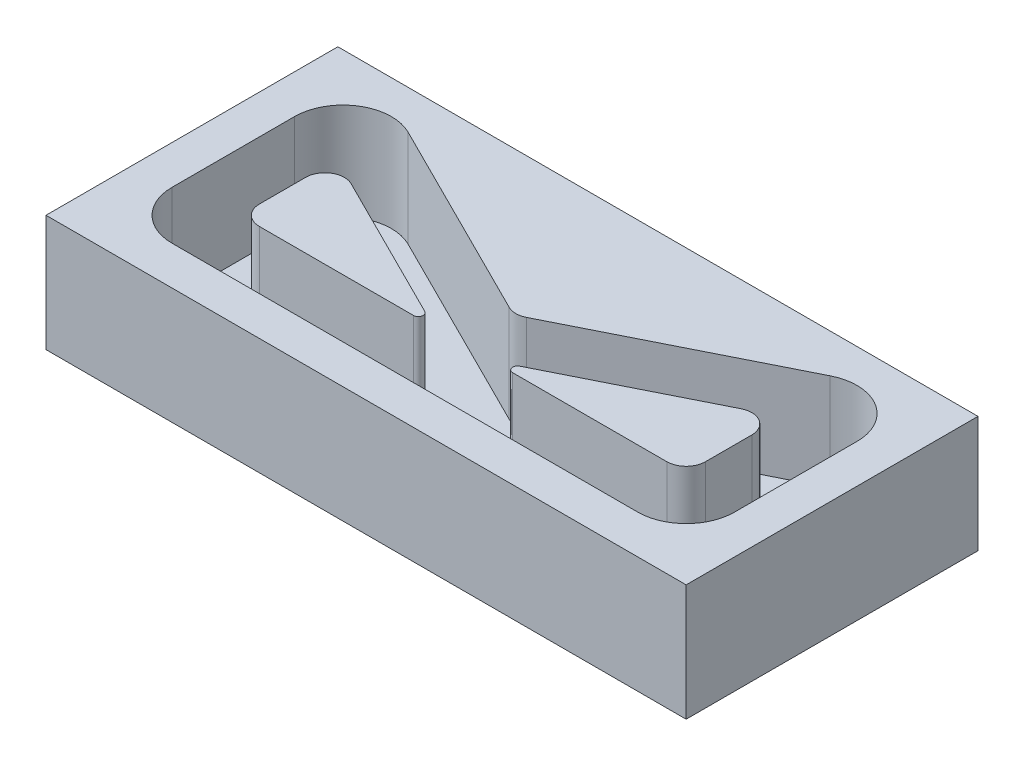
SolidWorks part; units mm, degrees
ref_plane "Front Plane" through (0, 0, 0) normal (0, 0, 1) x (1, 0, 0)
ref_plane "Top Plane" through (0, 0, 0) normal (0, 1, 0) x (1, 0, 0)
ref_plane "Right Plane" through (0, 0, 0) normal (1, 0, 0) x (0, 0, -1)
sketch "Sketch1" plane through (0, 0, 0) normal (0, 1, 0) x (1, 0, 0)
  line L0 (-0.9472, 0.4736) -> (-8.5528, 4.2764)
  line L1 (-10, 3.382) -> (-10, 1)
  line L2 (-9, 0) -> (-1.059, 0)
  line L3 (1.0528, 2.8277) -> (-9.382, 8.0451)
  line L4 (-13, 5.809) -> (-13, -0.5)
  line L5 (-10.5, -3) -> (13.5, -3)
  line L6 (-13, -3) -> (12.7082, -3) construction
  line L7 (-13, 9.8541) -> (-13, -3) construction
  line L8 (12.7082, -3) -> (-13, 9.8541) construction
  line L9 (-10, 5) -> (-10, 0) construction
  line L10 (0, 0) -> (-10, 5) construction
  line L11 (-10, 0) -> (0, 0) construction
  line L12 (1.5, 15.2524) -> (1.5, -18.7374) construction
  line L13 (12, 0) -> (4.059, 0)
  line L14 (3.9472, 0.4736) -> (11.5528, 4.2764)
  line L15 (1.9472, 2.8277) -> (12.382, 8.0451)
  line L16 (13, 3.382) -> (13, 1)
  line L17 (16, 5.809) -> (16, -0.5)
  line L18 (12.382, 8.0451) -> (-9.382, 8.0451) construction
  line L19 (-0.2764, 1.8152) -> (-7.882, 5.618) construction
  line L20 (-15, -5) -> (18, -5)
  line L21 (-15, -5) -> (-15, 10.0451)
  line L22 (-15, 10.0451) -> (18, 10.0451)
  line L23 (-12.9787, 6.1343) -> (1.5, -4.1568) construction
  line L24 (1.5, -4.1568) -> (15.9787, 6.1343) construction
  line L25 (18, -5) -> (18, 10.0451)
  line L26 (-15, -5) -> (18, 10.0451) construction
  line L27 (-15, 10.0451) -> (18, -5) construction
  line L28 (-11.5, 3.382) -> (-11.5, 1) construction
  line L29 (-9, -1.5) -> (-1.059, -1.5) construction
  line L30 (3.2764, 1.8152) -> (10.882, 5.618)
  line L31 (14.5, 3.382) -> (14.5, 1)
  line L32 (12, -1.5) -> (4.059, -1.5)
  circle A0 centre (1.5, 0.5061) radius 1.5831 construction
  circle A1 centre (-10.9351, 6.1728) radius 1.5 construction
  circle A2 centre (-11.0512, -1.07) radius 1.5 construction
  arc A3 (-10.5, -3) -> (-13, -0.5) centre (-10.5, -0.5) cw
  arc A4 (-9.382, 8.0451) -> (-13, 5.809) centre (-10.5, 5.809) ccw
  arc A5 (-10, 3.382) -> (-8.5528, 4.2764) centre (-9, 3.382) cw
  arc A6 (-9, 0) -> (-10, 1) centre (-9, 1) cw
  circle A7 centre (-4.84, -1.5) radius 1.5 construction
  circle A8 centre (-4.1195, 3.7368) radius 1.5 construction
  circle A9 centre (-11.5, 2.3936) radius 1.5 construction
  circle A10 centre (14.5, 2.3936) radius 1.5 construction
  circle A11 centre (7.1195, 3.7368) radius 1.5 construction
  circle A12 centre (7.84, -1.5) radius 1.5 construction
  circle A13 centre (14.0512, -1.07) radius 1.5 construction
  circle A14 centre (13.9351, 6.1728) radius 1.5 construction
  arc A15 (12, 0) -> (13, 1) centre (12, 1) ccw
  arc A16 (13, 3.382) -> (11.5528, 4.2764) centre (12, 3.382) ccw
  arc A17 (12.382, 8.0451) -> (16, 5.809) centre (13.5, 5.809) cw
  arc A18 (13.5, -3) -> (16, -0.5) centre (13.5, -0.5) ccw
  arc A19 (1.9472, 2.8277) -> (1.0528, 2.8277) centre (1.5, 3.7221) cw
  arc A20 (-1.059, 0) -> (-0.9472, 0.4736) centre (-1.059, 0.25) ccw
  arc A21 (3.9472, 0.4736) -> (4.059, 0) centre (4.059, 0.25) ccw
  arc A22 (-11.5, 3.382) -> (-7.882, 5.618) centre (-9, 3.382) cw construction
  arc A23 (-9, -1.5) -> (-11.5, 1) centre (-9, 1) cw construction
  arc A24 (-1.059, -1.5) -> (-0.2764, 1.8152) centre (-1.059, 0.25) ccw construction
  arc A25 (14.5, 3.382) -> (10.882, 5.618) centre (12, 3.382) ccw
  arc A26 (12, -1.5) -> (14.5, 1) centre (12, 1) ccw
  arc A27 (3.2764, 1.8152) -> (4.059, -1.5) centre (4.059, 0.25) ccw
  point P7 (1.5, 0.5061)
  point P23 (-10, 5)
  point P38 (1.5, -3)
  point P60 (13, 5)
  point P63 (1.5, 2.6041)
  point P69 (1.5, -4.1568)
  point P72 (1.5, 2.5225)
  dimension "D5" = 3
  dimension "D6" = 3
  dimension "D7" = 2.5
  dimension "D8" = 1
  dimension "D1" = 3
  dimension "D2" = 3
  dimension "D9" = 3
  dimension "D10" = 1
  dimension "D4" = 0.25
  dimension "D11" = 0.25
  dimension "D12" = 2
  dimension "D15" = 2
  dimension "D13" = 2
  dimension "D14" = 2
  dimension "D3" = 3
  dimension "D16" = 1.5
  dimension "D17" = 1.5
extrude "Boss-Extrude1" add sketch "Sketch1" along normal blind 5 contours L20 L25 L22 L21 A19 L15 A17 L17 A18 L5 A3 L4 A4 L3 | L2 A20 L0 A5 L1 A6 | L14 A21 L13 A15 L16 A16 | A25 L30 A27 L32 A26 L31
sketch "Sketch2" plane through (0, 0, 0) normal (0, -1, 0) x (1, 0, 0)
  line L4 (18, 5) -> (-15, 5)
  line L5 (-15, 5) -> (-15, -10.0451)
  line L6 (-15, -10.0451) -> (18, -10.0451)
  line L7 (18, -10.0451) -> (18, 5)
  line L8 (18, 5) -> (-15, 5)
  line L9 (-15, 5) -> (-15, -10.0451)
  line L10 (-15, -10.0451) -> (18, -10.0451)
  line L11 (18, -10.0451) -> (18, 5)
  dimension "D1" = 0
extrude "Boss-Extrude3" add sketch "Sketch2" along normal blind 1
